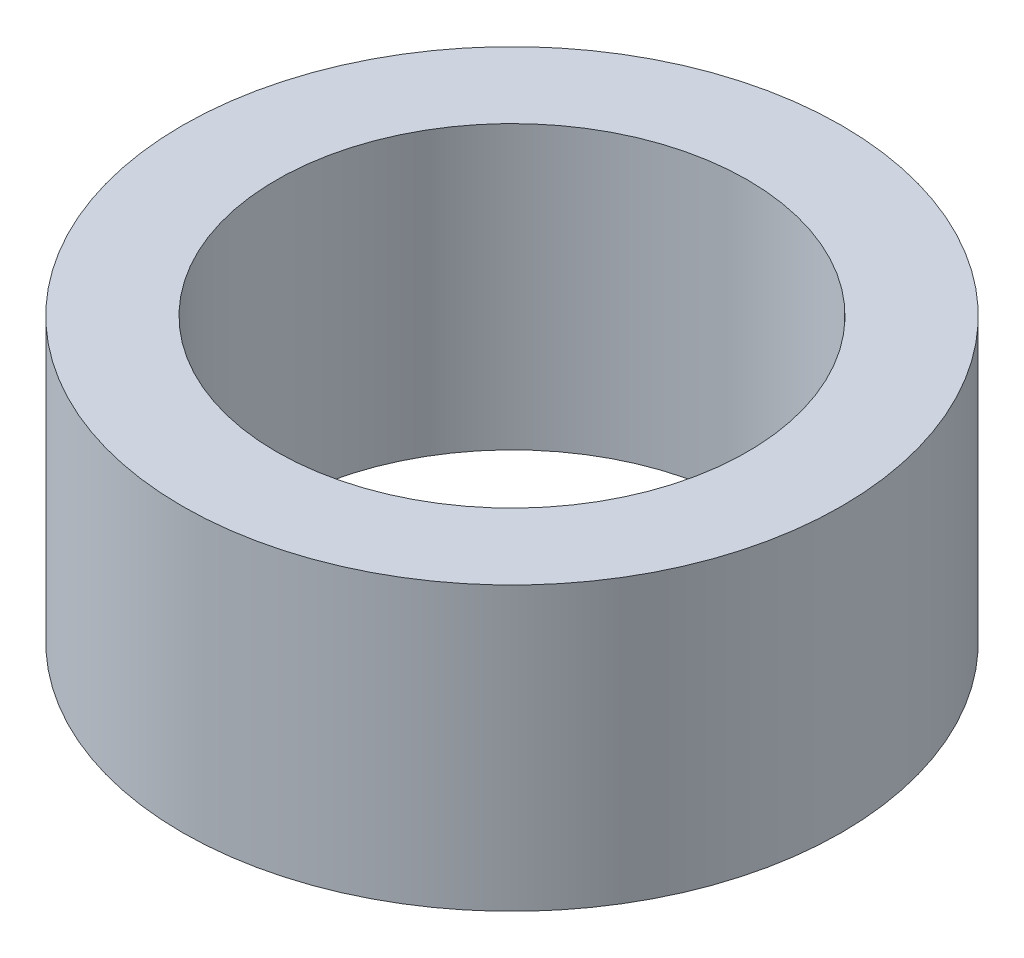
SolidWorks part; units mm, degrees
ref_plane "Alzado" through (0, 0, 0) normal (0, 0, 1) x (1, 0, 0)
ref_plane "Planta" through (0, 0, 0) normal (0, 1, 0) x (1, 0, 0)
ref_plane "Vista lateral" through (0, 0, 0) normal (1, 0, 0) x (0, 0, -1)
sketch "Croquis1" plane through (0, 0, 0) normal (0, 1, 0) x (1, 0, 0)
  circle A0 centre (0, 0) radius 12.5
  circle A1 centre (0, 0) radius 17.5
  dimension "D1" = 5
  dimension "D2" = 25
extrude "Saliente-Extruir1" add sketch "Croquis1" along normal blind 15
